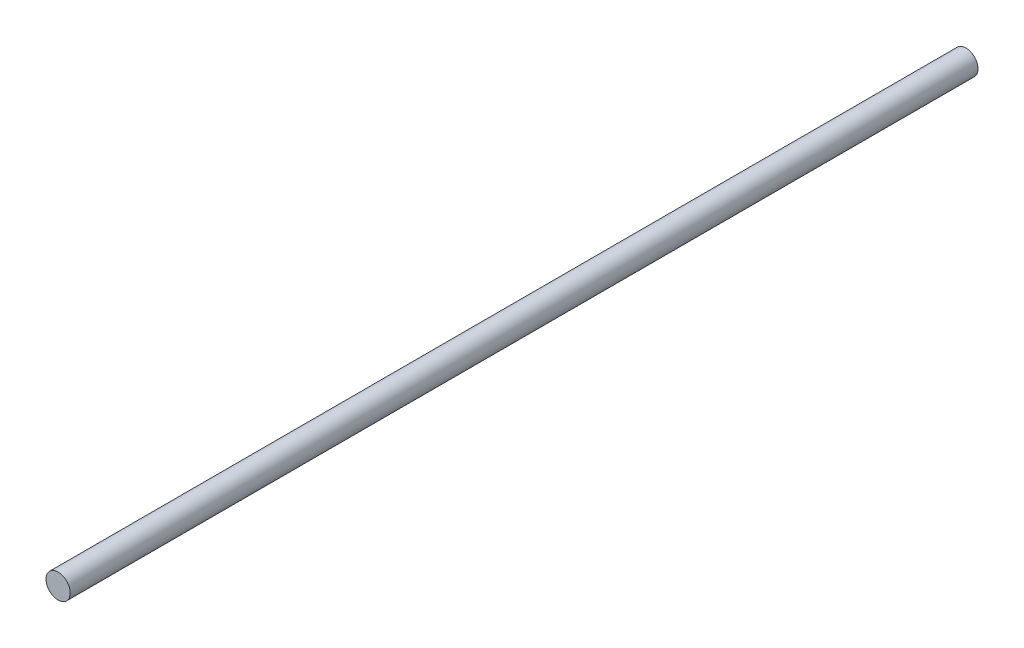
SolidWorks part; units mm, degrees
ref_plane "前视基准面" through (0, 0, 0) normal (0, 0, 1) x (1, 0, 0)
ref_plane "上视基准面" through (0, 0, 0) normal (0, 1, 0) x (1, 0, 0)
ref_plane "右视基准面" through (0, 0, 0) normal (1, 0, 0) x (0, 0, -1)
sketch "草图1" plane through (0, 0, 0) normal (0, 0, 1) x (1, 0, 0)
  circle A0 centre (0, 0) radius 4
extrude "凸台-拉伸1" add sketch "草图1" along normal blind 300
